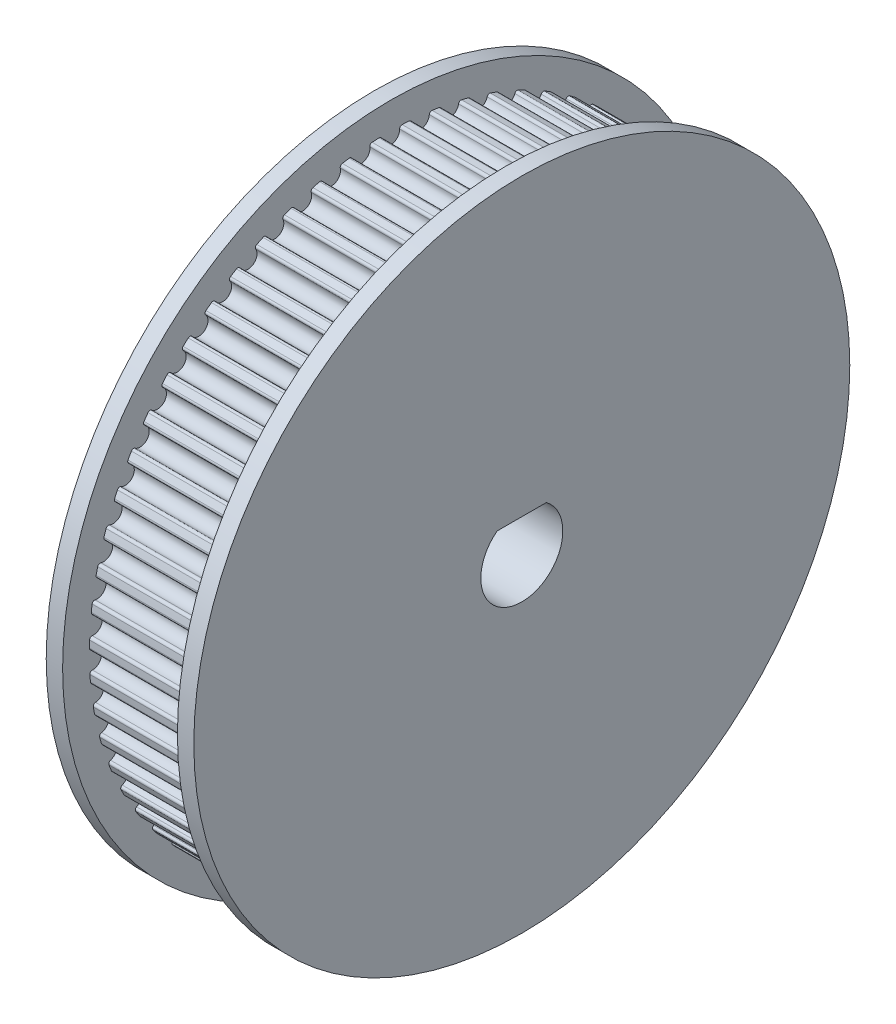
SolidWorks part; units mm, degrees
other "Markup1"
sketch "Sketch4" plane through (0, 30, 30) normal (-0.8111, 0.5766, 0.0979) x (0.0367, -0.117, 0.9925)
ref_plane "Front Plane" through (0, 0, 0) normal (0, 0, 1) x (1, 0, 0)
ref_plane "Top Plane" through (0, 0, 0) normal (0, 1, 0) x (1, 0, 0)
ref_plane "Right Plane" through (0, 0, 0) normal (1, 0, 0) x (0, 0, -1)
sketch "Sketch1" plane through (0, 0, 0) normal (0, 0, 1) x (1, 0, 0)
  line L8 (0, 0) -> (9, 0)
  line L9 (0, 0) -> (0, 20)
  line L10 (9, 0) -> (9, 20)
  line L11 (9, 20) -> (8, 20)
  line L12 (0, 20) -> (1, 20)
  line L13 (1, 20) -> (1, 18.37)
  line L14 (1, 18.37) -> (8, 18.37)
  line L15 (8, 18.37) -> (8, 20)
  dimension "D1" = 20
  dimension "D2" = 9
  dimension "D3" = 1
  dimension "D4" = 1
  dimension "D5" = 1.63
  dimension "D6" = 1.63
revolve "Revolve1" add sketch "Sketch1" angle 360 about L8
sketch "Sketch8" plane through (1, 0, 0) normal (1, 0, 0) x (0, 0, -1)
  arc A0 (0.5188, 18.3627) -> (-0.5188, 18.3627) centre (0, 0) ccw
  arc A1 (-0.5188, 18.3627) -> (0.5188, 18.3627) centre (0, 18.18) ccw
extrude "Cut-Extrude3" cut sketch "Sketch8" along normal blind 7 contours A1 A0
fillet "Fillet2" radius 0.15 2 edges at (4.5, 18.3627, 0.5188) (4.5, 18.3627, -0.5188)
pattern_circular "CirPattern2" count 63 over 360 about axis through (0, 0, 0) along (1, 0, 0) of "Cut-Extrude3", "Fillet2"
sketch "Sketch10" plane through (0, 0, 0) normal (0, 0, 1) x (1, 0, 0)
  line L0 (0, 0) -> (-7, 0)
  line L1 (-7, 0) -> (-7, 7.5)
  line L2 (-7, 7.5) -> (0, 7.5)
  line L3 (0, 20) -> (0, -20) construction
  line L4 (0, 7.5) -> (0, 0)
  dimension "D1" = 7
  dimension "D2" = 7.5
revolve "Revolve2" add sketch "Sketch10" angle 360 about L0
sketch "Sketch7" plane through (0, 0, 0) normal (-1, 0, 0) x (0, 0, 1)
  line L1 (0, 2) -> (1.5, 2)
  line L2 (0, 2) -> (-1.5, 2)
  arc A0 (-1.5, 2) -> (1.5, 2) centre (0, 0) ccw
  dimension "D1" = 5
  dimension "D2" = 1.5
  dimension "D3" = 1.5
extrude "Cut-Extrude4" cut sketch "Sketch7" against normal through all both and the other way through all
